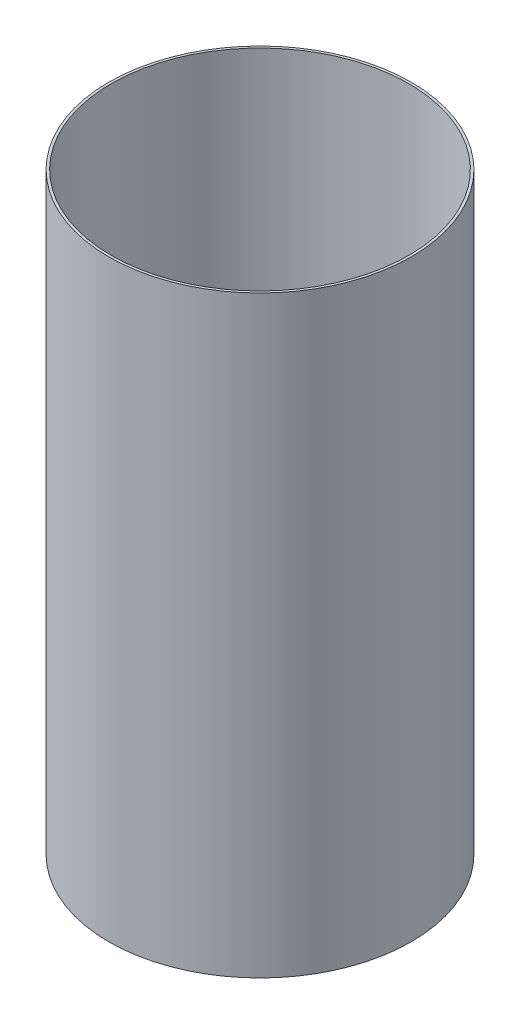
SolidWorks part; units mm, degrees
material "Hexcel AS4C (3000 Filaments)"
ref_plane "前视基准面" through (0, 0, 0) normal (0, 0, 1) x (1, 0, 0)
ref_plane "上视基准面" through (0, 0, 0) normal (0, 1, 0) x (1, 0, 0)
ref_plane "右视基准面" through (0, 0, 0) normal (1, 0, 0) x (0, 0, -1)
sketch "Sketch1" plane through (0, 0, 0) normal (0, 1, 0) x (1, 0, 0)
  circle A0 centre (0, 0) radius 76.454
  dimension "D1" = 152.908
extrude "Extrude-Thin2" add sketch "Sketch1" along normal blind 304.8 thin
sketch "Sketch2" plane through (0, 0, 0) normal (1, 0, 0) x (0, 0, -1)
  line L0 (0, 320.3693) -> (0, 0) construction
ref_plane "Plane1" through (76.454, 0, 0) normal (-1, 0, 0) x (0, 0, 1)
sketch "Sketch3" plane through (76.454, 0, 0) normal (-1, 0, 0) x (0, 0, 1)
  line L0 (0, 200320.3693) -> (0, -200000) construction
  circle A0 centre (0, 63.5) radius 3.302
  dimension "D1" = 6.604
  dimension "D2" = 63.5
extrude "Cut-Extrude2" cut sketch "Sketch3" along normal blind 2.54
pattern_circular "CirPattern2" count 3 every 120 about axis through (0, 0, 0) along (0, 1, 0) of "Cut-Extrude2"
